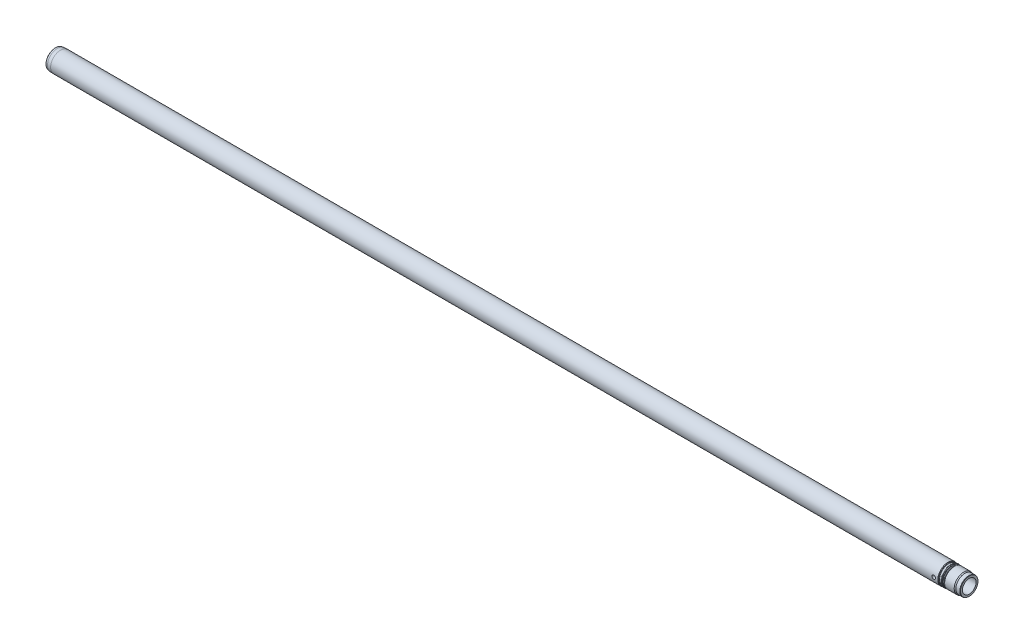
SolidWorks part; units mm, degrees
ref_plane "Front" through (0, 0, 0) normal (0, 0, 1) x (1, 0, 0)
ref_plane "Top" through (0, 0, 0) normal (0, 1, 0) x (1, 0, 0)
ref_plane "Right" through (0, 0, 0) normal (1, 0, 0) x (0, 0, -1)
sketch "Sketch1" plane through (0, 0, 0) normal (0, 0, 1) x (1, 0, 0)
  line L0 (0, 0) -> (2180, 0) construction
  line L1 (0, 21) -> (0, 23.5)
  line L2 (0.5, 24) -> (5, 24)
  line L3 (5, 24) -> (5, 24.75)
  line L4 (13, 25) -> (13, 24.75)
  line L5 (2284, 21.9226) -> (2283, 22.5)
  line L6 (5, 24.75) -> (13, 24.75)
  line L7 (2283, 22.5) -> (2273, 22.5)
  line L8 (13, 25) -> (2230.5, 25)
  line L9 (0, 21) -> (6.9282, 17)
  line L10 (6.9282, 17) -> (2284, 17)
  line L11 (2232, 24.134) -> (2232, 23.8)
  line L12 (2230.5, 25) -> (2232, 24.134)
  line L13 (2232.8, 23) -> (2237.2, 23)
  line L14 (2238, 23.8) -> (2238, 24.25)
  line L15 (2238.5, 24.75) -> (2239.5, 24.75)
  line L16 (2235, 23) -> (2235, 24) construction
  line L17 (2239.5, 24.75) -> (2241, 23.884)
  line L18 (2241, 23.884) -> (2241, 23.55)
  line L19 (2241.8, 22.75) -> (2244, 22.75)
  line L20 (2244, 22.75) -> (2246.4533, 24)
  line L21 (2246.4533, 24) -> (2270.4019, 24)
  line L22 (2284, 21.9226) -> (2284, 17)
  line L23 (0.5, 24) -> (0, 23.5)
  line L24 (2273, 22.5) -> (2270.4019, 24)
  arc A0 (2238.5, 24.75) -> (2238, 24.25) centre (2238.5, 24.25) ccw
  arc A2 (2241, 23.55) -> (2241.8, 22.75) centre (2241.8, 23.55) ccw
  arc A3 (2232, 23.8) -> (2232.8, 23) centre (2232.8, 23.8) ccw
  arc A4 (2237.2, 23) -> (2238, 23.8) centre (2237.2, 23.8) ccw
  point P33 (2232, 23)
  point P36 (2238, 23)
  dimension "D15" = 30
  dimension "D16" = 0.8
  dimension "D22" = 0.8
  dimension "D32" = 49.5
  dimension "D33" = 0.5
  dimension "D3" = 5
  dimension "D4" = 48
  dimension "D5" = 1.5
  dimension "D6" = 46
  dimension "D7" = 30
  dimension "D8" = 13
  dimension "D9" = 34
  dimension "D10" = 30
  dimension "D11" = 42
  dimension "D12" = 48
  dimension "D13" = 45.5
  dimension "D14" = 27
  dimension "D17" = 6
  dimension "D18" = 43
  dimension "D19" = 3
  dimension "D20" = 46
  dimension "D21" = 2284
  dimension "D23" = 50
  dimension "D24" = 49.5
  dimension "D25" = 0.5
  dimension "D26" = 45
  dimension "D27" = 30
  dimension "D28" = 45
  dimension "D29" = 1
  dimension "D30" = 11
  dimension "D31" = 1.5
revolve "Base-Revolve" add sketch "Sketch1" angle 360 about L0
cosmetic thread "Cosmetic Thread1" parameters "D2"=45.835
sketch "Sketch2" plane through (0, 0, 0) normal (0, 0, 1) x (1, 0, 0)
  line L0 (0, 0) -> (2284, 0) construction
  line L3 (2284, -21.9226) -> (2284, 21.9226) construction
  circle A0 centre (2220, 0) radius 4.5
  dimension "D2" = 9
  dimension "D1" = 64
extrude "Cut-Extrude1" cut sketch "Sketch2" against normal mid plane 100
